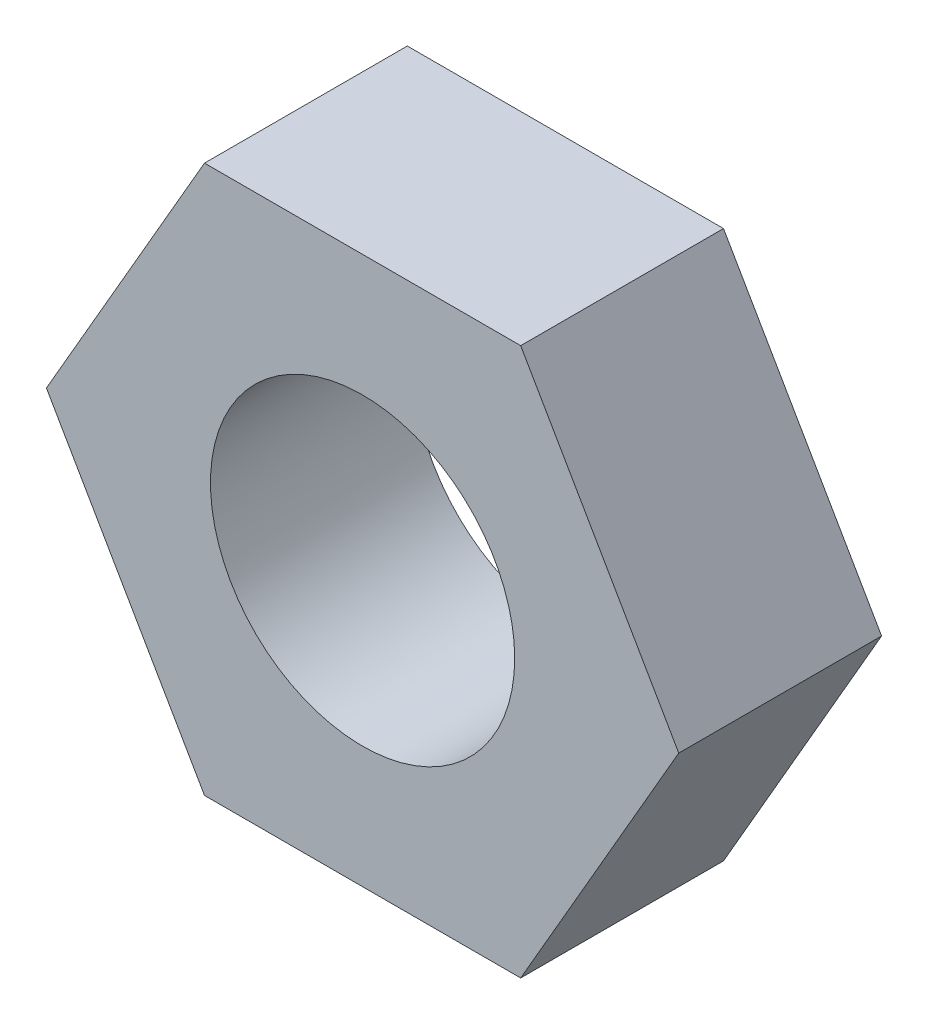
SolidWorks part; units mm, degrees
ref_plane "Front Plane" through (0, 0, 0) normal (0, 0, 1) x (1, 0, 0)
ref_plane "Top Plane" through (0, 0, 0) normal (0, 1, 0) x (1, 0, 0)
ref_plane "Right Plane" through (0, 0, 0) normal (1, 0, 0) x (0, 0, -1)
sketch "Sketch2" plane through (0, 0, 0) normal (0, 0, 1) x (1, 0, 0)
  line L1 (4.6765, 8.1) -> (-4.6765, 8.1)
  line L2 (-4.6765, 8.1) -> (-9.3531, 0)
  line L3 (-9.3531, 0) -> (-4.6765, -8.1)
  line L4 (-4.6765, -8.1) -> (4.6765, -8.1)
  line L5 (4.6765, -8.1) -> (9.3531, 0)
  line L6 (9.3531, 0) -> (4.6765, 8.1)
  circle A0 centre (0, 0) radius 4.5
  circle A1 centre (0, 0) radius 8.1 construction
  dimension "D1" = 9
  dimension "D2" = 16.2
extrude "Boss-Extrude1" add sketch "Sketch2" along normal blind 6
